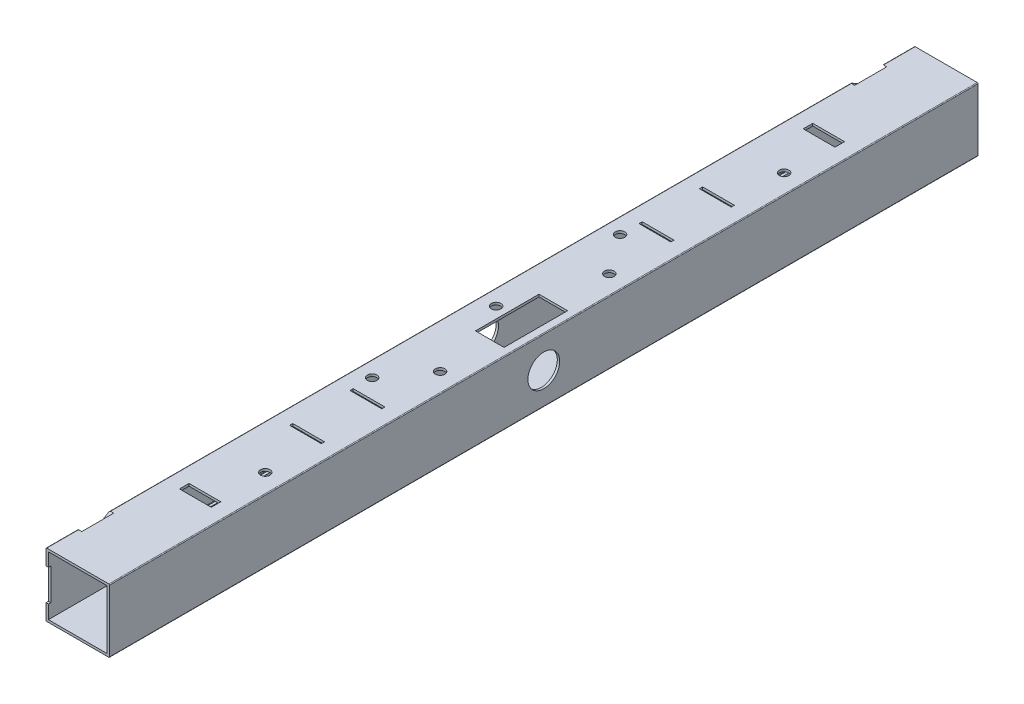
SolidWorks part; units mm, degrees
ref_plane "Front Plane" through (0, 0, 0) normal (0, 0, 1) x (1, 0, 0)
ref_plane "Top Plane" through (0, 0, 0) normal (0, 1, 0) x (1, 0, 0)
ref_plane "Right Plane" through (0, 0, 0) normal (1, 0, 0) x (0, 0, -1)
sketch "Sketch1" plane through (0, 0, 0) normal (0, 0, 1) x (1, 0, 0)
  line L0 (1.5, 1.5) -> (38.5, 1.5)
  line L1 (0.5, 0) -> (39.5, 0)
  line L2 (0, 0.5) -> (0, 39.5)
  line L3 (0.5, 40) -> (39.5, 40)
  line L4 (40, 0.5) -> (40, 39.5)
  line L5 (38.5, 1.5) -> (38.5, 38.5)
  line L6 (1.5, 38.5) -> (38.5, 38.5)
  line L7 (1.5, 1.5) -> (1.5, 38.5)
  arc A0 (0, 39.5) -> (0.5, 40) centre (0.5, 39.5) cw
  arc A1 (39.5, 40) -> (40, 39.5) centre (39.5, 39.5) cw
  arc A2 (39.5, 0) -> (40, 0.5) centre (39.5, 0.5) ccw
  arc A3 (0.5, 0) -> (0, 0.5) centre (0.5, 0.5) cw
  arc A4 (38.5, 1.5) -> (38.5, 1.5) centre (38.5, 1.5) ccw
  arc A5 (38.5, 38.5) -> (38.5, 38.5) centre (38.5, 38.5) cw
  arc A6 (1.5, 38.5) -> (1.5, 38.5) centre (1.5, 38.5) cw
  arc A7 (1.5, 1.5) -> (1.5, 1.5) centre (1.5, 1.5) cw
  point P13 (0, 0)
  dimension "D3" = 0.5
  dimension "D1" = 40
  dimension "D2" = 40
  dimension "D4" = 1.5
extrude "Boss-Extrude1" add sketch "Sketch1" along normal blind 546.5
sketch "Sketch2" plane through (0, 0, 0) normal (-1, 0, 0) x (0, 0, 1)
  line L0 (0, 39.5) -> (0, 0.5) construction
  line L1 (1.5, 30) -> (0, 30)
  line L2 (1.5, 30) -> (1.5, 10)
  line L3 (1.5, 10) -> (0, 10)
  line L4 (0, 30) -> (0, 10)
  line L5 (546.5, 40) -> (0, 40) construction
  line L6 (20, 0) -> (20, 40) construction
  line L7 (546.5, 0) -> (0, 0) construction
  line L8 (40, 30) -> (40, 10)
  line L9 (38.5, 10) -> (40, 10)
  line L10 (38.5, 30) -> (38.5, 10)
  line L11 (38.5, 30) -> (40, 30)
  line L12 (273.25, 39.5) -> (273.25, 0.5) construction
  line L13 (546.5, 39.5) -> (0, 39.5) construction
  line L14 (546.5, 0.5) -> (0, 0.5) construction
  line L15 (508, 30) -> (506.5, 30)
  line L16 (508, 30) -> (508, 10)
  line L17 (508, 10) -> (506.5, 10)
  line L18 (506.5, 30) -> (506.5, 10)
  line L19 (546.5, 30) -> (546.5, 10)
  line L20 (545, 10) -> (546.5, 10)
  line L21 (545, 30) -> (545, 10)
  line L22 (545, 30) -> (546.5, 30)
  line L23 (406.5, 12) -> (406.5, 14)
  line L24 (60, 12) -> (140, 12)
  line L25 (60, 12) -> (60, 14)
  line L26 (60, 14) -> (140, 14)
  line L27 (140, 12) -> (140, 14)
  line L28 (486.5, 14) -> (406.5, 14)
  line L29 (486.5, 12) -> (486.5, 14)
  line L30 (486.5, 12) -> (406.5, 12)
  line L32 (155, 6) -> (153, 6)
  line L33 (155, 6) -> (155, 12)
  line L34 (155, 12) -> (153, 12)
  line L35 (153, 6) -> (153, 12)
  line L36 (393.5, 6) -> (393.5, 12)
  line L37 (391.5, 12) -> (393.5, 12)
  line L38 (391.5, 6) -> (391.5, 12)
  line L39 (391.5, 6) -> (393.5, 6)
  line L40 (40.1, 40) -> (26.2436, 32)
  line L41 (20, 40) -> (40.1, 40)
  line L45 (20, 40) -> (6.1436, 32)
  line L46 (26.2436, 32) -> (6.1436, 32)
  line L47 (520.2564, 32) -> (540.3564, 32)
  line L48 (526.5, 40) -> (540.3564, 32)
  line L49 (526.5, 40) -> (506.4, 40)
  line L50 (506.4, 40) -> (520.2564, 32)
  point P44 (60, 13)
  dimension "D1" = 1.5
  dimension "D2" = 20
  dimension "D3" = 10
  dimension "D4" = 20
  dimension "D5" = 2
  dimension "D6" = 80
  dimension "D7" = 2
  dimension "D8" = 2
  dimension "D9" = 6
  dimension "D10" = 80
  dimension "D11" = 12
  dimension "D12" = 60
  dimension "D13" = 13
  dimension "D14" = 8
  dimension "D15" = 20.1
  dimension "D17" = 30
extrude "Cut-Extrude1" cut sketch "Sketch2" against normal blind 2.5
sketch "Sketch3" plane through (0, 40, 0) normal (0, 1, 0) x (1, 0, 0)
  line L1 (10, -466.5) -> (30, -466.5)
  line L2 (10, -466.5) -> (10, -472.5)
  line L3 (10, -472.5) -> (30, -472.5)
  line L4 (30, -466.5) -> (30, -472.5)
  line L5 (0, -546.5) -> (0, -527.366) construction
  line L7 (39.5, -546.5) -> (0.5, -546.5) construction
  line L8 (39.5, -273.25) -> (0.5, -273.25) construction
  line L9 (39.5, -546.5) -> (39.5, 0) construction
  line L11 (30, -80) -> (30, -74)
  line L12 (10, -74) -> (30, -74)
  line L13 (10, -80) -> (10, -74)
  line L14 (10, -80) -> (30, -80)
  dimension "D1" = 6
  dimension "D2" = 10
  dimension "D3" = 20
  dimension "D4" = 74
extrude "Cut-Extrude2" cut sketch "Sketch3" against normal blind 1.5
sketch "Sketch4" plane through (0, 40, 0) normal (0, 1, 0) x (1, 0, 0)
  line L1 (30, -143.3) -> (10, -143.3)
  line L2 (30, -143.3) -> (30, -145.3)
  line L3 (30, -145.3) -> (10, -145.3)
  line L4 (10, -143.3) -> (10, -145.3)
  line L5 (0, -507.266) -> (0, -39.234) construction
  line L6 (39.5, 0) -> (0.5, 0) construction
  line L7 (39.5, -163.3) -> (17.7447, -163.3) construction
  line L8 (39.5, -546.5) -> (39.5, 0) construction
  line L9 (10, -183.3) -> (10, -181.3)
  line L10 (30, -181.3) -> (10, -181.3)
  line L11 (30, -183.3) -> (30, -181.3)
  line L12 (30, -183.3) -> (10, -183.3)
  line L13 (0.5, -273.25) -> (39.5, -273.25) construction
  line L14 (0.5, -506.4) -> (0.5, -40.1) construction
  line L15 (30, -363.2) -> (10, -363.2)
  line L16 (30, -363.2) -> (30, -365.2)
  line L17 (30, -365.2) -> (10, -365.2)
  line L18 (10, -363.2) -> (10, -365.2)
  line L19 (10, -403.2) -> (10, -401.2)
  line L20 (30, -401.2) -> (10, -401.2)
  line L21 (30, -403.2) -> (30, -401.2)
  line L22 (30, -403.2) -> (10, -403.2)
  dimension "D1" = 2
  dimension "D2" = 10
  dimension "D3" = 20
  dimension "D4" = 143.3
  dimension "D5" = 20
extrude "Cut-Extrude3" cut sketch "Sketch4" against normal blind 2
sketch "Sketch5" plane through (0, 0, 0) normal (0, -1, 0) x (1, 0, 0)
  line L0 (0.5, 546.5) -> (39.5, 546.5) construction
  line L1 (0, 546.5) -> (0, 0) construction
  line L2 (39.5, 273.25) -> (0.5, 273.25) construction
  line L3 (39.5, 546.5) -> (39.5, 0) construction
  line L4 (0.5, 546.5) -> (0.5, 0) construction
  circle A0 centre (10, 351.25) radius 3
  circle A1 centre (10, 195.25) radius 3
  circle A2 centre (10, 273.25) radius 3
  point P16 (0, 0)
  dimension "D1" = 195.25
  dimension "D2" = 10
  dimension "D3" = 6
extrude "Cut-Extrude4" cut sketch "Sketch5" against normal through all
sketch "Sketch6" plane through (0, 0, 0) normal (0, -1, 0) x (-1, 0, 0)
  line L0 (-39.5, -273.25) -> (-0.5, -273.25) construction
  line L1 (-39.5, -546.5) -> (-39.5, 0) construction
  line L2 (-0.5, -546.5) -> (-0.5, 0) construction
  line L3 (-40, -546.5) -> (-40, 0) construction
  line L4 (-0.5, -546.5) -> (-39.5, -546.5) construction
  circle A0 centre (-28, -436.5) radius 3
  circle A1 centre (-28, -326.5) radius 3
  circle A2 centre (-28, -220) radius 3
  circle A3 centre (-28, -110) radius 3
  point P14 (0, 0)
  dimension "D1" = 12
  dimension "D2" = 6
  dimension "D3" = 110
  dimension "D4" = 110
extrude "Cut-Extrude5" cut sketch "Sketch6" against normal through all
sketch "Sketch7" plane through (0, 0, 0) normal (-1, 0, 0) x (0, 0, 1)
  line L0 (273.25, 39.5) -> (273.25, 0.5) construction
  line L1 (507.266, 39.5) -> (39.234, 39.5) construction
  line L2 (546.5, 0.5) -> (0, 0.5) construction
  circle A0 centre (273.25, 20) radius 10
  point P8 (0, 0)
  point P9 (273.25, 20)
  point P10 (0, 0)
  dimension "D1" = 20
extrude "Cut-Extrude6" cut sketch "Sketch7" against normal through all
sketch "Sketch8" plane through (0, 40, 0) normal (0, 1, 0) x (1, 0, 0)
  line L0 (40, -273.25) -> (35, -273.25) construction
  line L1 (35, -293.25) -> (17, -293.25)
  line L2 (35, -293.25) -> (35, -253.25)
  line L3 (35, -253.25) -> (17, -253.25)
  line L4 (17, -293.25) -> (17, -253.25)
  line L5 (40, -546.5) -> (40, 0) construction
  line L6 (39.5, -546.5) -> (39.5, 0) construction
  point P10 (39.5, -273.25)
  dimension "D1" = 40
  dimension "D2" = 18
  dimension "D3" = 5
extrude "Cut-Extrude7" cut sketch "Sketch8" against normal blind 10
